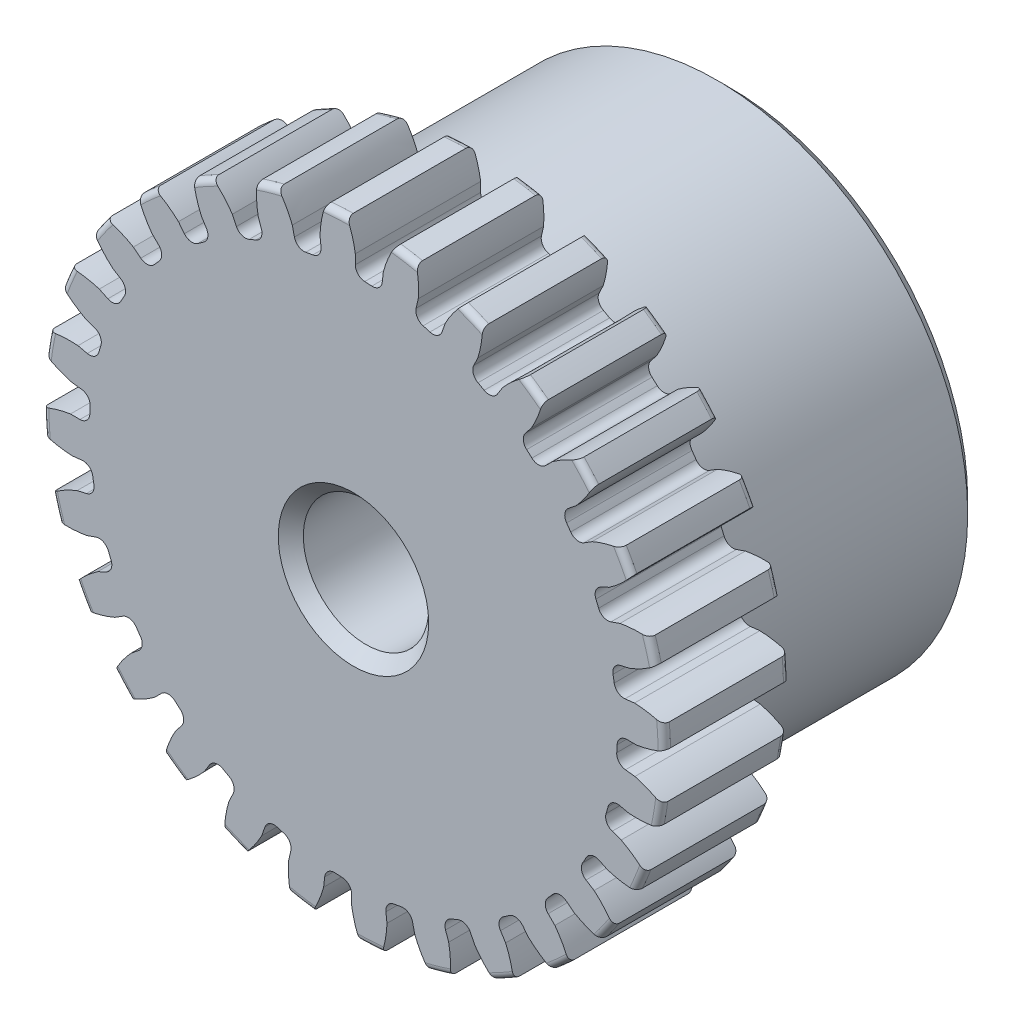
SolidWorks part; units mm, degrees
ref_plane "Front" through (0, 0, 0) normal (0, 0, 1) x (1, 0, 0)
ref_plane "Top" through (0, 0, 0) normal (0, 1, 0) x (1, 0, 0)
ref_plane "Right" through (0, 0, 0) normal (1, 0, 0) x (0, 0, -1)
sketch "Sketch1" plane through (0, 0, 0) normal (0, 0, 1) x (1, 0, 0)
  line L0 (-355.6, 0) -> (355.6, 0) construction
  circle A0 centre (0, 0) radius 7.874
  circle A1 centre (0, 0) radius 7.4041 construction
  circle A3 centre (0, 0) radius 6.6841 construction
  dimension "D3" = 0.4699
  dimension "D1" = 1.1899
extrude "Boss-Extrude1" add sketch "Sketch1" against normal blind 3.175
sketch "Sketch2" plane through (0, 0, 0) normal (1, 0, 0) x (0, 0, -1)
  line L0 (3.175, 0) -> (9.525, 0)
  line L1 (3.175, 0) -> (3.175, 6.35)
  line L2 (3.175, 6.35) -> (9.525, 6.35)
  line L3 (9.525, 6.35) -> (9.525, 0)
  point P5 (9.525, -6.35)
  point P6 (0, -7.874)
  point P7 (3.175, -7.874)
  point P9 (0, 7.874)
revolve "Revolve1" add sketch "Sketch2" angle 360 mid plane about L0
fillet "Fillet2" radius 0.1575 3 edges at (7.874, 0, -3.175) (7.874, 0, 0) (6.35, 0, -3.175)
sketch "Sketch3" plane through (0, 0, 0) normal (0, 0, 1) x (1, 0, 0)
  line L0 (0, 0) -> (0, 7.874) construction
  line L1 (-1.7948, 6.9399) -> (0, 7.4041)
  line L2 (-9.5921, 7.4041) -> (9.5921, 7.4041) construction
  line L3 (-9.2865, 5.0024) -> (9.2865, 9.8058) construction
  line L4 (-1.7948, 6.9399) -> (0, 0) construction
  line L5 (-4.5779, 5.516) -> (0, 0) construction
  line L6 (-4.5779, 5.516) -> (-0.7458, 8.6964) construction
  line L7 (-1.2515, 7.0582) -> (0, 0) construction
  line L8 (-1.2515, 7.0582) -> (0.0263, 7.2847) construction
  arc A0 (-1.7948, 6.9399) -> (-4.5779, 5.516) centre (0, 0) ccw
  circle A1 centre (0, 0) radius 7.4041 construction
  circle A2 centre (0, 0) radius 7.1683 construction
  arc A3 (-1.7948, 6.9399) -> (-1.2515, 7.0582) centre (0, 0) cw
  circle A4 centre (0, 0) radius 7.874 construction
  point P6 (0, 7.4041)
  dimension "D1" = 1.8538
  dimension "D3" = 4.98
  dimension "D5" = 1.2977
  dimension "D2" = 3.1515
  dimension "D4" = 0.5562
sketch "Sketch4" plane through (0, 0, 0) normal (0, 0, 1) x (1, 0, 0)
  line L0 (0, 0) -> (0.4145, 7.3808) construction
  line L1 (0.0464, 7.1681) -> (0.0464, 6.6839)
  line L2 (0, 7.4041) -> (0.829, 7.3575) construction
  line L3 (0.7565, 7.1282) -> (0.7022, 6.6471)
  line L4 (0.0464, 6.6839) -> (0, 0) construction
  line L5 (0, 0) -> (0, 7.874) construction
  line L6 (-4.5779, 5.516) -> (-0.7458, 8.6964) construction
  line L7 (-4.5779, 5.516) -> (-0.7458, 8.6964) construction
  arc A0 (0.7022, 6.6471) -> (0.0464, 6.6839) centre (0, 0) ccw
  arc A1 (0, 7.4041) -> (0.829, 7.3575) centre (0, 0) cw construction
  circle A2 centre (0, 0) radius 7.4041 construction
  circle A3 centre (0, 0) radius 7.1683 construction
  circle A4 centre (0, 0) radius 6.6841 construction
  arc A5 (1.7148, 8.5582) -> (-0.7458, 8.6964) centre (0, 0) ccw
  spline S0 degree 2 poles (-0.7458, 8.6964) (-0.0823, 8.0256) (0.0464, 7.1681) knots 0 0 0 1 1 1
  spline S1 degree 2 poles (1.7148, 8.5582) (0.9804, 7.9659) (0.7565, 7.1282) knots 0 0 0 1 1 1
  dimension "D1" = 0.8307
extrude "Cut-Extrude1" cut sketch "Sketch4" against normal through all
fillet "Fillet1" radius 0.2492 2 edges at (0.7022, 6.6471, -1.5875) (0.0464, 6.6839, -1.5875)
pattern_circular "CirPattern1" count 28 over 360 about axis through (0, 0, -3.175) along (0, 0, 1) of "Cut-Extrude1", "Fillet1"
sketch "Sketch5" plane through (0, 0, 0) normal (0, 0, 1) x (1, 0, 0)
  circle A0 centre (0, 0) radius 1.5875
  circle A1 centre (0, 0) radius 1.5875 construction
  dimension "Bore Min" = 3.175
  dimension "Bore Max" = 3.175
extrude "Cut-Extrude2" cut sketch "Sketch5" against normal through all
chamfer "Chamfer1" distance 0.3175 angle 45 3 edges at (6.35, 0, -9.525) (1.5875, 0, 0) (1.5875, 0, -9.525)
sketch "Pitch Dia" plane through (0, 0, 0) normal (0, 0, 1) x (1, 0, 0)
  circle A0 centre (0, 0) radius 7.4041 construction
  circle A1 centre (0, 0) radius 7.4041 construction
equation "\"D1@Boss-Extrude1\" = \"Face Wd@Sketch2\""
equation "\"D2@Sketch3\" = \"D1@Sketch3\"*1.7"
equation "\"D3@Sketch3\" = \"D1@Sketch3\"+\"D2@Sketch3\"-.001"
equation "\"D4@Sketch3\" = \"D1@Sketch3\"*.3"
equation "\"D5@Sketch3\" = \"D1@Sketch3\"-\"D4@Sketch3\""
equation "\"D1@Sketch4\" = 1.5708/(\"Number of Teeth@Sketch1\"/\"Ptich Dia@Sketch1\")"
equation "\"D1@Chamfer1\" = \"B Hub Dia@Sketch2\"*.025"
equation "\"D1@CirPattern1\" = \"Number of Teeth@Sketch1\""
equation "\"D1@Fillet1\" = \"D1@Sketch4\"*.3"
equation "\"D1@Fillet2\" = \"OD@Sketch1\"*.01"
equation "\"D1@Sketch1\" = 2.250/(\"Number of Teeth@Sketch1\"/\"Ptich Dia@Sketch1\")"
